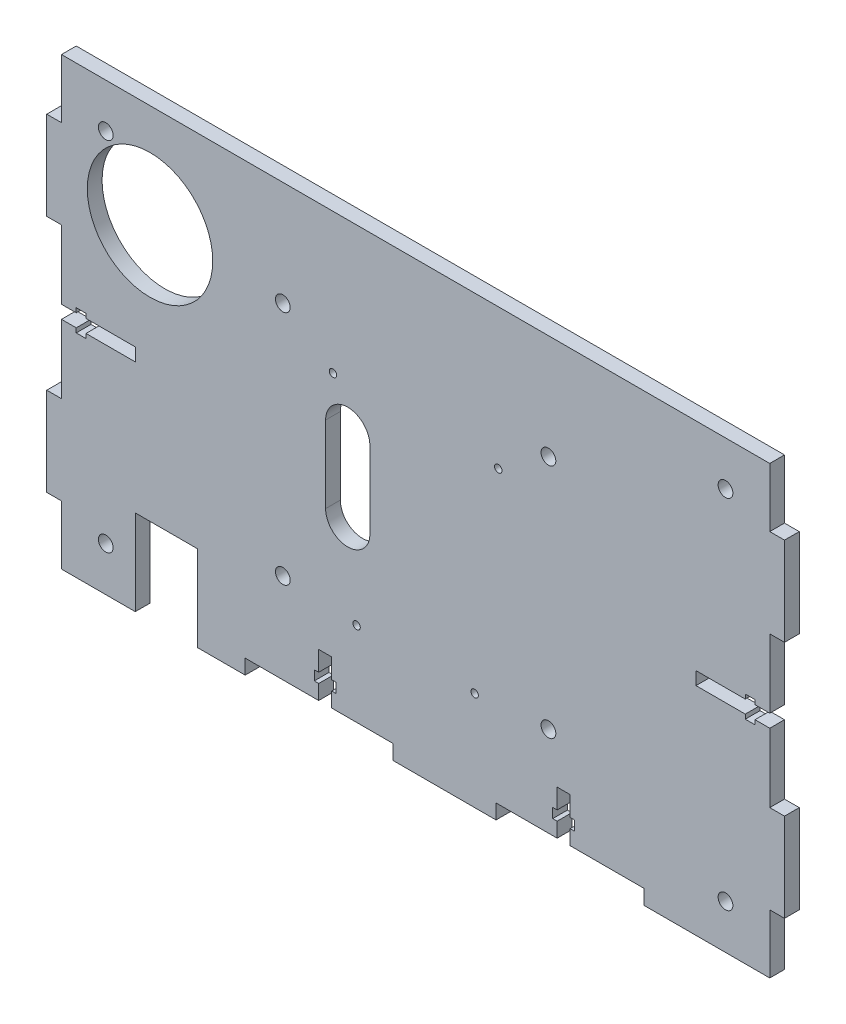
SolidWorks part; units mm, degrees
ref_plane "Front Plane" through (0, 0, 0) normal (0, 0, 1) x (1, 0, 0)
ref_plane "Top Plane" through (0, 0, 0) normal (0, 1, 0) x (1, 0, 0)
ref_plane "Right Plane" through (0, 0, 0) normal (1, 0, 0) x (0, 0, -1)
sketch "Sketch1" plane through (0, 0, 0) normal (0, 0, 1) x (1, 0, 0)
  line L1 (-120, 75.5) -> (120, 75.5)
  line L2 (-120, 75.5) -> (-120, -75.5)
  line L3 (-120, -75.5) -> (120, -75.5)
  line L4 (120, 75.5) -> (120, -75.5)
  dimension "D1" = 240
  dimension "D2" = 120
  dimension "D3" = 151
  dimension "D4" = 75.5
extrude "Boss-Extrude1" add sketch "Sketch1" along normal blind 5
sketch "Sketch2" plane through (0, 0, 0) normal (0, 0, -1) x (-1, 0, 0)
  circle A1 centre (28, 28) radius 1.25
  circle A3 centre (-28, 28) radius 1.25
  circle A5 centre (20, -42) radius 1.25
  circle A7 centre (-20, -42) radius 1.25
extrude "Cut-Extrude1" cut sketch "Sketch2" against normal blind 5
sketch "Sketch5" plane through (0, 0, 0) normal (0, 0, -1) x (-1, 0, 0)
  line L0 (23, -13) -> (23, 13) construction
  line L1 (15.5, -13) -> (15.5, 13)
  line L2 (30.5, -13) -> (30.5, 13)
  arc A0 (15.5, -13) -> (30.5, -13) centre (23, -13) ccw
  arc A1 (30.5, 13) -> (15.5, 13) centre (23, 13) ccw
  circle A3 centre (28, 28) radius 1.25 construction
  point P2 (23, 0)
  dimension "D1" = 5
  dimension "D2" = 15
  dimension "D3" = 15
  dimension "D4" = 26
extrude "Cut-Extrude2" cut sketch "Sketch5" against normal blind 10
sketch "Sketch6" plane through (0, 0, 0) normal (0, 0, -1) x (-1, 0, 0)
  circle A1 centre (-105, 60.5) radius 2.5
  circle A3 centre (-105, -60.5) radius 2.5
  circle A5 centre (105, -60.5) radius 2.5
  circle A7 centre (105, 60.5) radius 2.5
extrude "Cut-Extrude3" cut sketch "Sketch6" against normal blind 10
sketch "Sketch7" plane through (0, 0, 0) normal (0, 0, -1) x (-1, 0, 0)
  line L0 (0, 0) -> (0, -54.3684) construction
  line L1 (0, 0) -> (71.9806, 0) construction
  circle A0 centre (45, 40) radius 2.5
  circle A1 centre (45, -40) radius 2.5
  circle A2 centre (-45, 40) radius 2.5
  circle A3 centre (-45, -40) radius 2.5
  dimension "D2" = 5
  dimension "D3" = 5
  dimension "D7" = 5
  dimension "D8" = 5
  dimension "D1" = 40
  dimension "D4" = 45
  dimension "D5" = 45
  dimension "D6" = 40
extrude "Cut-Extrude4" cut sketch "Sketch7" against normal blind 10
sketch "Sketch8" plane through (0, 0, 0) normal (0, 0, -1) x (-1, 0, 0)
  line L0 (120, 75.5) -> (120, -75.5) construction
  line L2 (120, -75.5) -> (-120, -75.5) construction
  line L8 (95, -75.5) -> (95, -46.5)
  line L9 (73.9, -75.5) -> (95, -75.5)
  line L10 (73.9, -46.5) -> (73.9, -75.5)
  line L11 (95, -46.5) -> (73.9, -46.5)
  dimension "D1" = 25
  dimension "D2" = 21.1
  dimension "D3" = 29
extrude "Cut-Extrude5" cut sketch "Sketch8" against normal blind 10
sketch "Sketch9" plane through (0, 0, 0) normal (0, 0, -1) x (-1, 0, 0)
  line L0 (120, 75.5) -> (120, -75.5) construction
  line L1 (120, 55.5) -> (125, 55.5)
  line L2 (120, 55.5) -> (120, 25.5)
  line L3 (120, 25.5) -> (125, 25.5)
  line L4 (125, 55.5) -> (125, 25.5)
  line L5 (-120, 75.5) -> (120, 75.5) construction
  line L6 (120, -25.5) -> (125, -25.5)
  line L7 (120, -25.5) -> (120, -55.5)
  line L8 (120, -55.5) -> (125, -55.5)
  line L9 (125, -25.5) -> (125, -55.5)
  line L11 (120, -75.5) -> (95, -75.5) construction
  line L12 (0, 0) -> (0, -172.8228) construction
  line L13 (-125, -25.5) -> (-125, -55.5)
  line L14 (-120, -55.5) -> (-125, -55.5)
  line L15 (-120, -25.5) -> (-120, -55.5)
  line L16 (-120, -25.5) -> (-125, -25.5)
  line L17 (-125, 55.5) -> (-125, 25.5)
  line L18 (-120, 25.5) -> (-125, 25.5)
  line L19 (-120, 55.5) -> (-120, 25.5)
  line L20 (-120, 55.5) -> (-125, 55.5)
  dimension "D1" = 5
  dimension "D2" = 5
  dimension "D3" = 20
  dimension "D4" = 30
  dimension "D5" = 20
  dimension "D6" = 30
extrude "Boss-Extrude2" add sketch "Sketch9" against normal blind 5
sketch "Sketch10" plane through (0, 0, 0) normal (0, 0, -1) x (-1, 0, 0)
  line L0 (-120, 0) -> (-90.1273, 0) construction
  line L1 (-120, -25.5) -> (-120, 25.5) construction
  line L2 (-120, 2.2) -> (-115, 2.2)
  line L3 (-115, 2.2) -> (-115, 3.7)
  line L4 (-115, 3.7) -> (-111.7, 3.7)
  line L5 (-111.7, 3.7) -> (-111.7, 2.2)
  line L6 (-111.7, 2.2) -> (-95, 2.2)
  line L7 (-95, 2.2) -> (-95, -2.2)
  line L8 (-95, -2.2) -> (-111.7, -2.2)
  line L9 (-111.7, -2.2) -> (-111.7, -3.7)
  line L10 (-111.7, -3.7) -> (-115, -3.7)
  line L11 (-115, -3.7) -> (-115, -2.2)
  line L12 (-115, -2.2) -> (-120, -2.2)
  line L13 (0, 0) -> (0, -23.4808) construction
  line L14 (120, 0) -> (90.1273, 0) construction
  line L15 (115, -2.2) -> (120, -2.2)
  line L16 (115, -3.7) -> (115, -2.2)
  line L17 (111.7, -3.7) -> (115, -3.7)
  line L18 (111.7, -2.2) -> (111.7, -3.7)
  line L19 (95, -2.2) -> (111.7, -2.2)
  line L20 (95, 2.2) -> (95, -2.2)
  line L21 (111.7, 2.2) -> (95, 2.2)
  line L22 (111.7, 3.7) -> (111.7, 2.2)
  line L23 (115, 3.7) -> (111.7, 3.7)
  line L24 (115, 2.2) -> (115, 3.7)
  line L25 (120, 2.2) -> (115, 2.2)
  line L26 (-120, -2.2) -> (-120, 2.2)
  line L27 (120, 2.2) -> (120, -2.2)
  dimension "D1" = 4.4
  dimension "D2" = 1.5
  dimension "D3" = 3.3
  dimension "D4" = 5
  dimension "D5" = 25
extrude "Cut-Extrude6" cut sketch "Sketch10" against normal blind 5
sketch "Sketch11" plane through (0, 0, 0) normal (0, 0, -1) x (-1, 0, 0)
  line L0 (120, -55.5) -> (120, -75.5) construction
  line L1 (7.75, -70.5) -> (57.75, -70.5)
  line L2 (7.75, -75.5) -> (57.75, -75.5)
  line L4 (-77.35, -75.5) -> (-27.25, -75.5)
  line L5 (57.75, -70.5) -> (57.75, -75.5)
  line L6 (-77.35, -70.5) -> (-27.25, -70.5)
  line L7 (-77.35, -70.5) -> (-77.35, -75.5)
  line L8 (-27.25, -70.5) -> (-27.25, -75.5)
  line L9 (7.75, -70.5) -> (7.75, -75.5)
  dimension "D1" = 50.1
  dimension "D2" = 50
  dimension "D3" = 62.25
  dimension "D4" = 35
extrude "Cut-Extrude7" cut sketch "Sketch11" against normal blind 10
sketch "Sketch12" plane through (0, 0, 0) normal (0, 0, -1) x (-1, 0, 0)
  line L0 (-52.35, -55.5) -> (-52.35, -62.2)
  line L1 (-52.35, -55.5) -> (-47.95, -55.5)
  line L2 (-47.95, -55.5) -> (-47.95, -62.2)
  line L3 (-47.95, -62.2) -> (-46.45, -62.2)
  line L4 (-46.45, -62.2) -> (-46.45, -65.5)
  line L5 (-46.45, -65.5) -> (-47.95, -65.5)
  line L6 (-47.95, -65.5) -> (-47.95, -70.5)
  line L7 (-52.35, -62.2) -> (-53.85, -62.2)
  line L8 (-53.85, -62.2) -> (-53.85, -65.5)
  line L9 (-53.85, -65.5) -> (-52.35, -65.5)
  line L10 (-52.35, -65.5) -> (-52.35, -70.5)
  line L11 (-52.35, -70.5) -> (-47.95, -70.5)
  line L12 (-50.15, -70.5) -> (-50.15, -36.9371) construction
  line L13 (-27.25, -70.5) -> (-77.35, -70.5) construction
  line L14 (-77.35, -70.5) -> (-77.35, -75.5) construction
  line L15 (-9.75, -75.5) -> (-9.75, -45.5639) construction
  line L16 (7.75, -75.5) -> (-27.25, -75.5) construction
  line L17 (30.65, -70.5) -> (30.65, -36.9371) construction
  line L18 (32.85, -70.5) -> (28.45, -70.5)
  line L19 (32.85, -65.5) -> (32.85, -70.5)
  line L20 (34.35, -65.5) -> (32.85, -65.5)
  line L21 (34.35, -62.2) -> (34.35, -65.5)
  line L22 (32.85, -62.2) -> (34.35, -62.2)
  line L23 (28.45, -65.5) -> (28.45, -70.5)
  line L24 (26.95, -65.5) -> (28.45, -65.5)
  line L25 (26.95, -62.2) -> (26.95, -65.5)
  line L26 (28.45, -62.2) -> (26.95, -62.2)
  line L27 (28.45, -55.5) -> (28.45, -62.2)
  line L28 (32.85, -55.5) -> (28.45, -55.5)
  line L29 (32.85, -55.5) -> (32.85, -62.2)
  dimension "D1" = 4.4
  dimension "D2" = 1.5
  dimension "D3" = 3.3
  dimension "D4" = 15
  dimension "D5" = 25
extrude "Cut-Extrude8" cut sketch "Sketch12" against normal blind 10
sketch "Sketch15" plane through (0, 0, 0) normal (0, 0, -1) x (-1, 0, 0)
  line L1 (-120, 75.5) -> (120, 75.5) construction
  line L2 (125, 25.5) -> (125, 55.5) construction
  circle A0 centre (90, 40.5) radius 21.25
  point P3 (0, 0)
  dimension "D3" = 42.5
  dimension "D1" = 35
  dimension "D2" = 35
extrude "Cut-Extrude9" cut sketch "Sketch15" against normal blind 10
